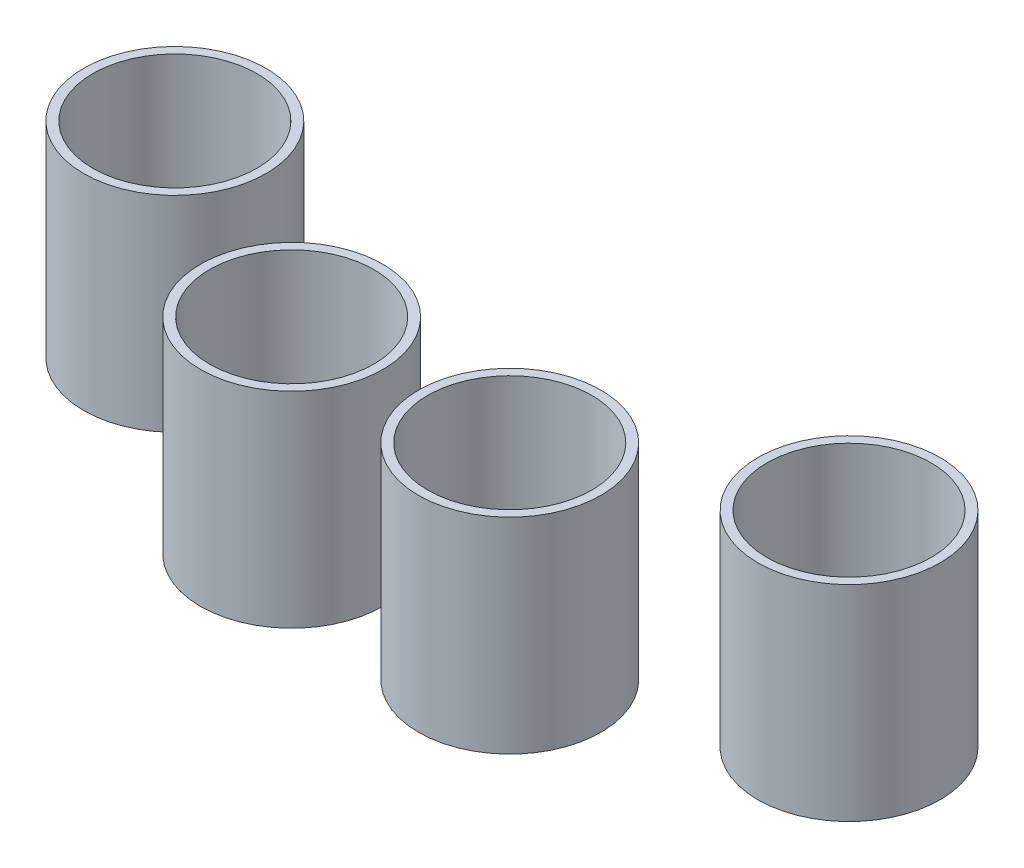
SolidWorks part; units mm, degrees
ref_plane "Front Plane" through (0, 0, 0) normal (0, 0, 1) x (1, 0, 0)
ref_plane "Top Plane" through (0, 0, 0) normal (0, 1, 0) x (1, 0, 0)
ref_plane "Right Plane" through (0, 0, 0) normal (1, 0, 0) x (0, 0, -1)
sketch "Sketch1" plane through (0, 0, 0) normal (0, 1, 0) x (1, 0, 0)
  line L0 (421.0671, 0) -> (-421.0671, 0) construction
  line L1 (-147.8412, -176.1902) -> (147.8412, -176.1902) construction
  line L2 (0, 0) -> (-147.8412, -176.1902) construction
  line L3 (0, 0) -> (-47.8197, -224.9739) construction
  line L4 (0, 0) -> (147.8412, -176.1902) construction
  line L5 (0, 0) -> (47.8197, -224.9739) construction
  circle A0 centre (-147.8412, -176.1902) radius 40
  circle A1 centre (-47.8197, -224.9739) radius 40
  circle A2 centre (47.8197, -224.9739) radius 40
  circle A3 centre (147.8412, -176.1902) radius 40
  dimension "D5" = 80
  dimension "D1" = 230
  dimension "D2" = 50
  dimension "D3" = 230
  dimension "D4" = 28
  dimension "D6" = 28
  dimension "D7" = 130
extrude "Boss-Extrude2" add sketch "Sketch1" along normal blind 90
sketch "Sketch2" plane through (0, 90, 0) normal (0, 1, 0) x (1, 0, 0)
  circle A2 centre (-47.8197, -224.9739) radius 36
  circle A3 centre (-147.8412, -176.1902) radius 36
  circle A4 centre (-147.8412, -176.1902) radius 36
  circle A5 centre (47.8197, -224.9739) radius 36
  circle A6 centre (147.8412, -176.1902) radius 36
  circle A7 centre (-47.8197, -224.9739) radius 40 construction
  circle A8 centre (47.8197, -224.9739) radius 40 construction
  circle A9 centre (147.8412, -176.1902) radius 40 construction
  dimension "D1" = 4
extrude "Cut-Extrude1" cut sketch "Sketch2" against normal blind 80
